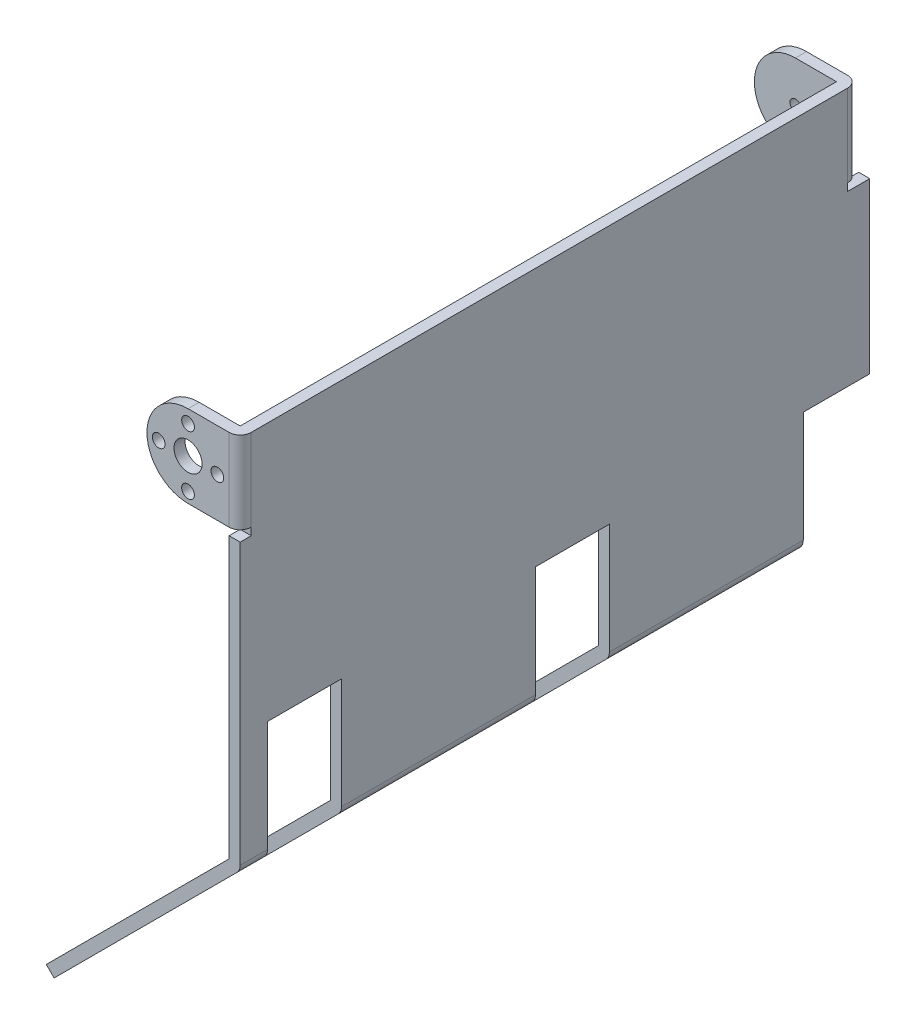
SolidWorks part; units mm, degrees
ref_plane "Plan de face" through (0, 0, 0) normal (0, 0, 1) x (1, 0, 0)
ref_plane "Plan de dessus" through (0, 0, 0) normal (0, 1, 0) x (1, 0, 0)
ref_plane "Plan de droite" through (0, 0, 0) normal (1, 0, 0) x (0, 0, -1)
sketch "Esquisse1" plane through (0, 0, 0) normal (0, 0, 1) x (1, 0, 0)
  line L0 (-6.8083, -1.1007) -> (-56.3058, -50.5981)
  line L1 (-6.8083, 98.8993) -> (-3.8083, 98.8993)
  line L2 (-6.8083, 98.8993) -> (-6.8083, -1.1007)
  line L3 (-56.3058, -50.5981) -> (-54.1845, -52.7195)
  line L4 (-3.8083, 98.8993) -> (-3.8083, -1.1007)
  line L5 (-54.1845, -52.7195) -> (-4.687, -3.222)
  arc A0 (-4.687, -3.222) -> (-3.8083, -1.1007) centre (-6.8083, -1.1007) ccw
  dimension "D1" = 3
  dimension "D2" = 100
  dimension "D3" = 100
  dimension "D4" = 135
  dimension "D5" = 70
  dimension "D7" = 70
extrude "Boss.-Extru.1" add sketch "Esquisse1" along normal blind 167.45
sketch "Esquisse2" plane through (-3.8083, 0, 0) normal (1, 0, 0) x (0, 0, -1)
  line L0 (0, -1.1007) -> (0, 98.8993) construction
  line L1 (-167.45, -1.1007) -> (-167.45, 98.8993) construction
  line L2 (-160, 28.8993) -> (-140, 28.8993)
  line L3 (-160, 28.8993) -> (-160, -52.7195)
  line L4 (-160, -52.7195) -> (-140, -52.7195)
  line L5 (-15, 28.8993) -> (0, 28.8993)
  line L6 (-140, 28.8993) -> (-140, -52.7195)
  line L7 (-167.45, 98.8993) -> (0, 98.8993) construction
  line L8 (-15, 28.8993) -> (-15, -52.7195)
  line L9 (-87.5, 28.8993) -> (-67.5, 28.8993)
  line L10 (-87.5, 28.8993) -> (-87.5, -52.7195)
  line L11 (-87.5, -52.7195) -> (-67.5, -52.7195)
  line L12 (-67.5, 28.8993) -> (-67.5, -52.7195)
  line L13 (-15, -52.7195) -> (0, -52.7195)
  line L14 (0, 28.8993) -> (0, -52.7195)
  line L15 (-167.45, -52.7195) -> (0, -52.7195) construction
  line L17 (-167.45, 76.6693) -> (-164.45, 76.6693)
  line L18 (-167.45, 76.6693) -> (-167.45, 74.6693)
  line L19 (-167.45, 74.6693) -> (-164.45, 74.6693)
  line L20 (-164.45, 76.6693) -> (-164.45, 74.6693)
  line L21 (0, 74.6693) -> (-3, 74.6693)
  line L22 (0, 74.6693) -> (0, 76.6693)
  line L23 (0, 76.6693) -> (-3, 76.6693)
  line L24 (-3, 74.6693) -> (-3, 76.6693)
  dimension "D1" = 20
  dimension "D2" = 7.45
  dimension "D3" = 70
  dimension "D4" = 52.5
  dimension "D5" = 20
  dimension "D6" = 15
  dimension "D7" = 0
  dimension "D10" = 22.23
  dimension "D11" = 2
  dimension "D12" = 3
  dimension "D13" = 3
extrude "Enlèv. mat.-Extru.1" cut sketch "Esquisse2" against normal through all
sketch "Esquisse3" plane through (0, 0, 167.45) normal (0, 0, 1) x (1, 0, 0)
  line L0 (-6.8083, 98.8993) -> (-17.9233, 98.8993)
  line L1 (-6.8083, 76.6693) -> (-17.9233, 76.6693)
  line L3 (-17.9233, 98.8993) -> (-17.9233, 76.6693) construction
  line L4 (-6.8083, 98.8993) -> (-6.8083, 76.6693)
  arc A0 (-17.9233, 98.8993) -> (-17.9233, 76.6693) centre (-17.9233, 87.7843) ccw
  circle A1 centre (-17.9233, 87.7843) radius 3.8
  circle A2 centre (-25.8633, 87.4534) radius 1.725
  circle A3 centre (-17.9233, 95.3934) radius 1.725
  circle A4 centre (-9.9833, 87.4534) radius 1.725
  circle A5 centre (-17.9233, 79.5134) radius 1.725
  point P7 (-17.9233, 87.4534)
  dimension "D5" = 7.6
  dimension "D6" = 3.45
  dimension "D1" = 11.115
  dimension "D2" = 22.23
  dimension "D3" = 7.94
  dimension "D4" = 7.94
  dimension "D8" = 4
extrude "Boss.-Extru.2" add sketch "Esquisse3" against normal blind 3
sketch "Esquisse4" plane through (0, 0, 0) normal (0, 0, -1) x (-1, 0, 0)
  line L0 (6.8083, 98.8993) -> (17.9233, 98.8993)
  line L1 (6.8083, 76.6693) -> (17.9233, 76.6693)
  line L2 (17.9233, 98.8993) -> (17.9233, 76.6693) construction
  line L3 (6.8083, 98.8993) -> (6.8083, 76.6693)
  arc A0 (17.9233, 98.8993) -> (17.9233, 76.6693) centre (17.9233, 87.7843) cw
  circle A1 centre (17.9233, 87.7843) radius 1.5
  point P8 (15.9825, 87.4534)
  dimension "D3" = 3
  dimension "D1" = 11.115
  dimension "D2" = 22.23
extrude "Boss.-Extru.3" add sketch "Esquisse4" against normal blind 3
sketch "Esquisse5" plane through (0, 0, 0) normal (0, 0, -1) x (-1, 0, 0)
  line L0 (6.8083, 28.8993) -> (6.8083, 74.6693)
  line L1 (3.8083, 28.8993) -> (6.8083, 28.8993)
  line L2 (6.8083, 74.6693) -> (3.8083, 74.6693)
  line L3 (3.8083, 74.6693) -> (3.8083, 28.8993)
  dimension "D1" = 45.77
extrude "Boss.-Extru.4" add sketch "Esquisse5" along normal blind 3
fillet "Congé1" radius 3 2 edges at (-3.8083, 87.7843, 0) (-3.8083, 87.7843, 167.45)
